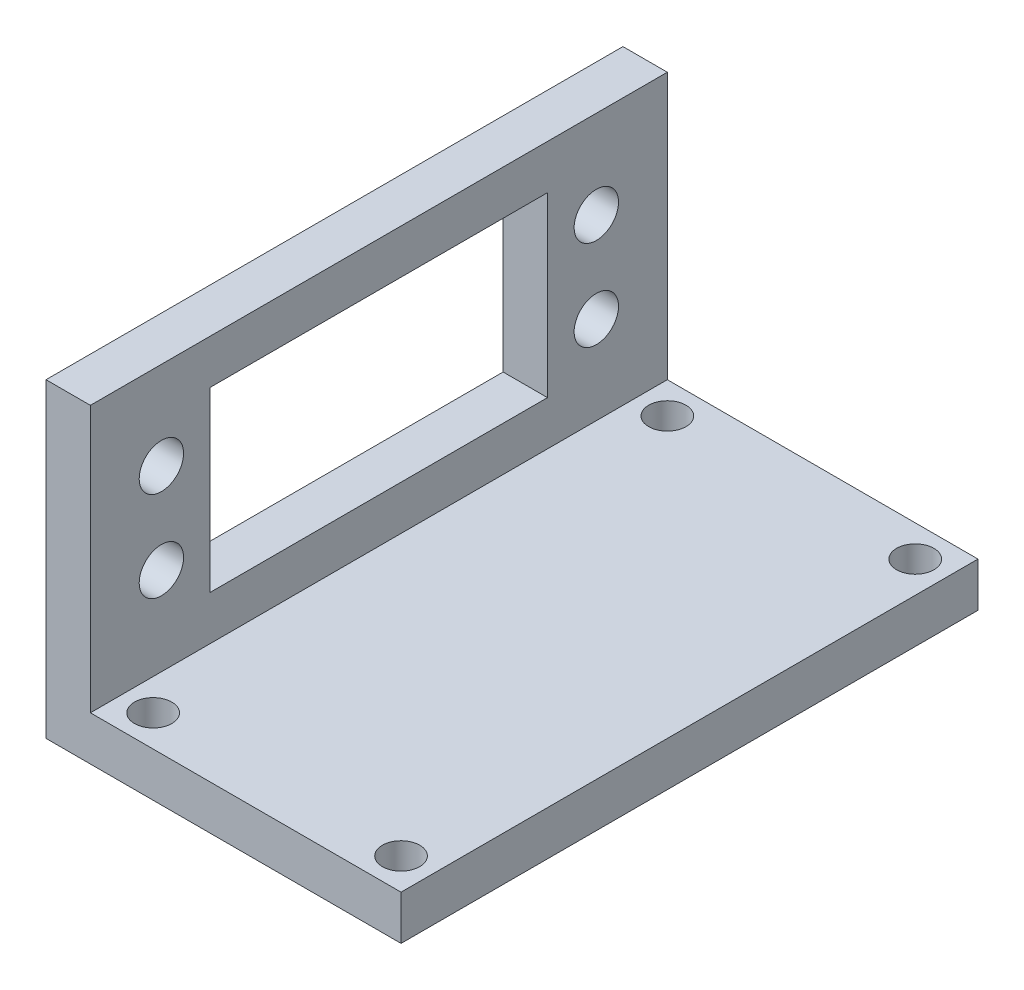
SolidWorks part; units mm, degrees
ref_plane "Front Plane" through (0, 0, 0) normal (0, 0, 1) x (1, 0, 0)
ref_plane "Top Plane" through (0, 0, 0) normal (0, 1, 0) x (1, 0, 0)
ref_plane "Right Plane" through (0, 0, 0) normal (1, 0, 0) x (0, 0, -1)
sketch "Sketch1" plane through (0, 0, 0) normal (0, 0, 1) x (1, 0, 0)
  line L0 (0, 0) -> (0, 35)
  line L1 (0, 35) -> (5, 35)
  line L2 (5, 35) -> (5, 5)
  line L3 (5, 5) -> (40, 5)
  line L4 (40, 5) -> (40, 0)
  line L5 (40, 0) -> (0, 0)
  dimension "D1" = 5
  dimension "D2" = 5
  dimension "D3" = 40
  dimension "D4" = 35
extrude "Boss-Extrude1" add sketch "Sketch1" along normal blind 65
sketch "Sketch2" plane through (5, 0, 0) normal (1, 0, 0) x (0, 0, -1)
  circle A0 centre (-8, 25.08) radius 2.5
  circle A1 centre (-8, 14.92) radius 2.5
  circle A2 centre (-57, 25.08) radius 2.5
  circle A3 centre (-57, 14.92) radius 2.5
extrude "Cut-Extrude1" cut sketch "Sketch2" against normal blind 10
sketch "Sketch3" plane through (0, 0, 0) normal (-1, 0, 0) x (0, 0, 1)
  line L20 (15.5, 10) -> (13.5, 10) construction
  line L21 (51.5, 30) -> (13.5, 30)
  line L22 (51.5, 30) -> (51.5, 10)
  line L23 (51.5, 10) -> (13.5, 10)
  line L24 (13.5, 30) -> (13.5, 10)
  line L25 (51.5, 30) -> (13.5, 10) construction
  line L26 (51.5, 10) -> (13.5, 30) construction
  point P0 (32.5, 20)
extrude "Cut-Extrude2" cut sketch "Sketch3" against normal blind 10
sketch "Sketch6" plane through (0, 5, 0) normal (0, 1, 0) x (1, 0, 0)
  line L0 (5, 0) -> (40, -65) construction
  line L1 (40, 0) -> (36.4645, -3.5355) construction
  line L2 (40, 0) -> (5, 0) construction
  line L3 (22.5, -32.5) -> (22.5, -23.6927) construction
  line L4 (22.5, -32.5) -> (28.521, -32.5) construction
  circle A0 centre (36.4645, -3.5355) radius 2.1
  circle A1 centre (8.5355, -3.5355) radius 2.1
  circle A2 centre (36.4645, -61.4645) radius 2.1
  circle A3 centre (8.5355, -61.4645) radius 2.1
  dimension "D3" = 4.2
  dimension "D1" = 45
  dimension "D2" = 5
extrude "Cut-Extrude5" cut sketch "Sketch6" against normal through all
